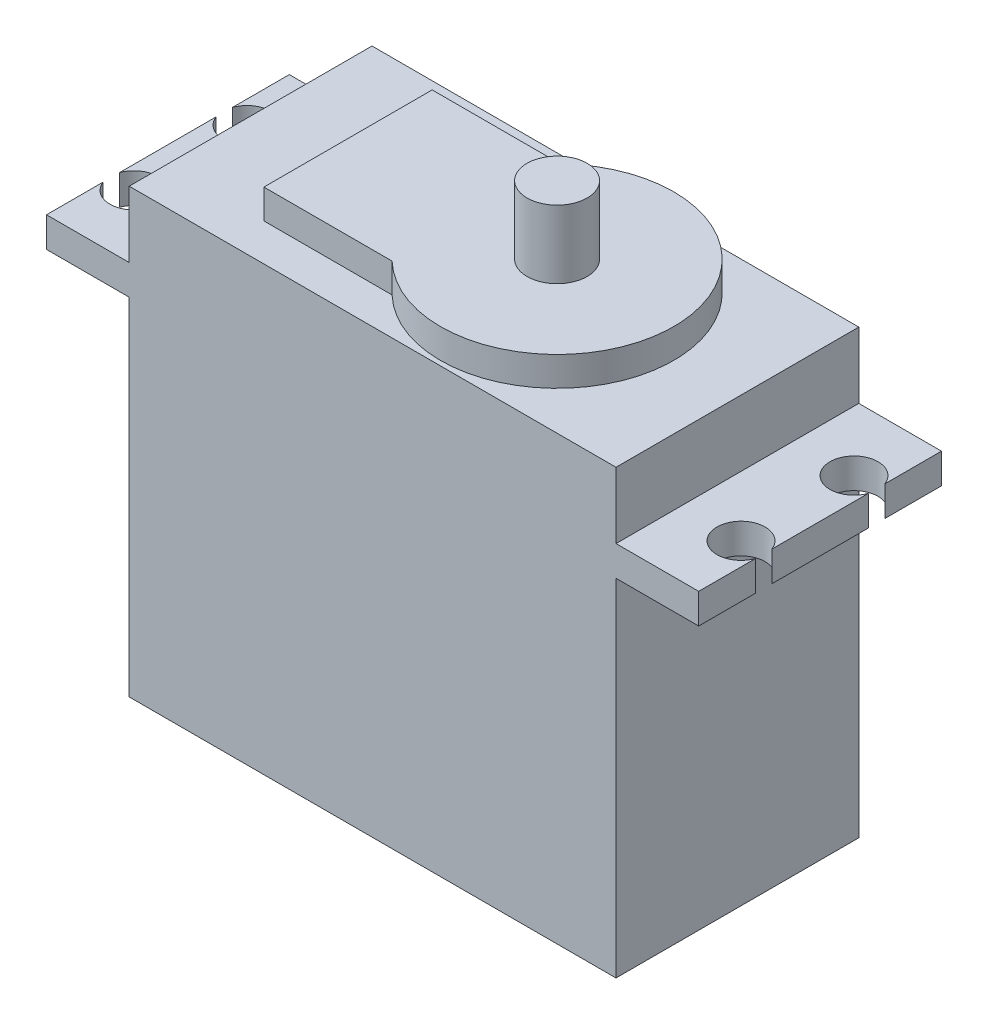
SolidWorks part; units mm, degrees
ref_plane "Alzado" through (0, 0, 0) normal (0, 0, 1) x (1, 0, 0)
ref_plane "Planta" through (0, 0, 0) normal (0, 1, 0) x (1, 0, 0)
ref_plane "Vista lateral" through (0, 0, 0) normal (1, 0, 0) x (0, 0, -1)
sketch "Croquis1" plane through (0, 0, 0) normal (0, 1, 0) x (1, 0, 0)
  line L1 (0, 0) -> (40.5, 0)
  line L2 (0, 0) -> (0, 20.2)
  line L3 (0, 20.2) -> (40.5, 20.2)
  line L4 (40.5, 0) -> (40.5, 20.2)
  dimension "D1" = 40.5
  dimension "D2" = 20.2
extrude "Saliente-Extruir1" add sketch "Croquis1" along normal blind 36.8
sketch "Croquis2" plane through (0, 36.8, 0) normal (0, 1, 0) x (1, 0, 0)
  line L1 (40.5, 0) -> (40.5, 20.2) construction
  line L2 (40.5, 10.1) -> (0, 10.1) construction
  line L3 (0, 20.2) -> (0, 0) construction
  line L9 (0, 17.1) -> (40.5, 17.1) construction
  line L10 (0, 3.1) -> (40.5, 3.1) construction
  line L12 (8.1065, 17.1) -> (8.1065, 3.1)
  line L13 (8.1065, 3.1) -> (18.7702, 3.1)
  line L14 (8.1065, 17.1) -> (18.7702, 17.1)
  circle A1 centre (25.5, 10.1) radius 9.7103
  dimension "D1" = 15
  dimension "D2" = 7
  dimension "D3" = 7
extrude "Saliente-Extruir2" add sketch "Croquis2" along normal blind 2.44 contours A1 | A1 L14 L12 L13
sketch "Croquis3" plane through (0, 39.24, 0) normal (0, 1, 0) x (1, 0, 0)
  circle A0 centre (25.5, 10.1) radius 2.5
  dimension "D1" = 5
extrude "Saliente-Extruir3" add sketch "Croquis3" along normal blind 5.66
sketch "Croquis4" plane through (0, 0, 0) normal (-1, 0, 0) x (0, 0, 1)
  line L0 (-20.2, 36.8) -> (-20.2, 0) construction
  line L1 (-20.2, 31.3) -> (0, 31.3)
  line L2 (-20.2, 31.3) -> (-20.2, 28.8)
  line L3 (-20.2, 28.8) -> (0, 28.8)
  line L4 (0, 31.3) -> (0, 28.8)
  line L5 (0, 36.8) -> (0, 0) construction
  line L8 (-20.2, 36.8) -> (0, 36.8) construction
  line L9 (-20.2, 0) -> (0, 0) construction
  dimension "D1" = 8
  dimension "D2" = 2.5
  dimension "D3" = 28.8
extrude "Saliente-Extruir4" add sketch "Croquis4" along normal blind 6.88
sketch "Croquis5" plane through (40.5, 0, 0) normal (1, 0, 0) x (0, 0, -1)
  line L0 (0, 36.8) -> (0, 0) construction
  line L1 (0, 31.3) -> (20.2, 31.3)
  line L2 (0, 31.3) -> (0, 28.8)
  line L3 (0, 28.8) -> (20.2, 28.8)
  line L4 (20.2, 31.3) -> (20.2, 28.8)
  line L5 (20.2, 36.8) -> (20.2, 0) construction
  line L9 (0, 0) -> (20.2, 0) construction
  dimension "D1" = 2.5
  dimension "D2" = 28.8
extrude "Saliente-Extruir5" add sketch "Croquis5" along normal blind 6.88
sketch "Croquis6" plane through (0, 31.3, 0) normal (0, 1, 0) x (1, 0, 0)
  line L0 (0, 20.2) -> (0, 0) construction
  line L1 (-6.88, 20.2) -> (-6.88, 0)
  line L2 (40.5, 20.2) -> (40.5, 0) construction
  line L3 (-6.88, 10.1) -> (47.38, 10.1) construction
  line L4 (47.38, 20.2) -> (47.38, 0) construction
  line L5 (47.38, 20.2) -> (47.38, 0)
  arc A0 (-6.88, 14.1177) -> (-6.88, 15.4823) centre (-5, 14.8) ccw
  arc A1 (-6.88, 4.7177) -> (-6.88, 6.0823) centre (-5, 5.4) ccw
  arc A2 (47.38, 15.4823) -> (47.38, 14.1177) centre (45.5, 14.8) ccw
  arc A3 (47.38, 6.0823) -> (47.38, 4.7177) centre (45.5, 5.4) ccw
  dimension "D1" = 4
  dimension "D2" = 4
  dimension "D5" = 4
  dimension "D6" = 4
  dimension "D3" = 5
  dimension "D4" = 5
  dimension "D7" = 5
  dimension "D8" = 5
  dimension "D9" = 4.7
  dimension "D10" = 4.7
  dimension "D11" = 4.7
  dimension "D12" = 4.7
extrude "Cortar-Extruir1" cut sketch "Croquis6" against normal through all contours L1 A1 | L1 A0 | L5 A2 | L5 A3
